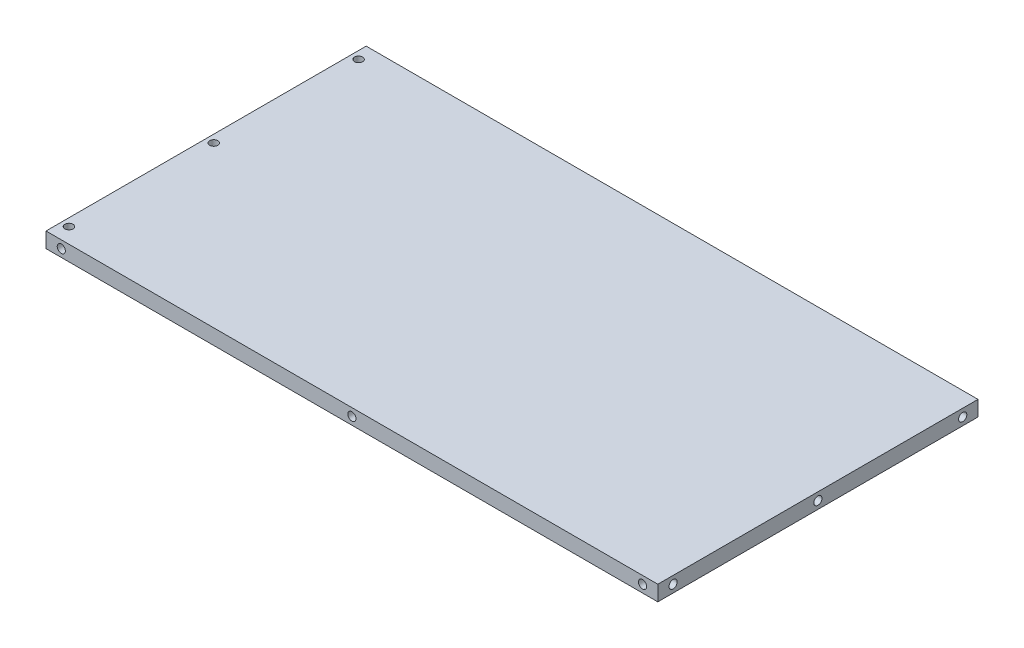
SolidWorks part; units mm, degrees
material "Oak"
ref_plane "Front Plane" through (0, 0, 0) normal (0, 0, 1) x (1, 0, 0)
ref_plane "Top Plane" through (0, 0, 0) normal (0, 1, 0) x (1, 0, 0)
ref_plane "Right Plane" through (0, 0, 0) normal (1, 0, 0) x (0, 0, -1)
sketch "Sketch1" plane through (0, 0, 0) normal (0, 1, 0) x (1, 0, 0)
  line L1 (-300, -157) -> (300, -157)
  line L2 (-300, -157) -> (-300, 157)
  line L3 (-300, 157) -> (300, 157)
  line L4 (300, -157) -> (300, 157)
  line L5 (-300, -157) -> (300, 157) construction
  line L6 (-300, 157) -> (300, -157) construction
  point P0 (0, 0)
  dimension "D1" = 600
  dimension "D2" = 314
extrude "Boss-Extrude1" add sketch "Sketch1" along normal blind 15
sketch "Sketch2" plane through (0, 15, 0) normal (0, 1, 0) x (1, 0, 0)
  line L0 (-285, 157) -> (-285, -157) construction
  line L1 (300, 157) -> (-300, 157) construction
  line L2 (-300, -157) -> (300, -157) construction
  line L3 (-300, 157) -> (-300, -157) construction
  line L4 (-300, 157) -> (-285, 157) construction
  line L5 (-292.5, 157) -> (-292.5, 146) construction
  line L6 (-300, -142) -> (-285, -142) construction
  circle A0 centre (-292.5, 142) radius 4
  dimension "D1" = 15
  dimension "D4" = 8
  dimension "D2" = 15
  dimension "D3" = 11
extrude "Cut-Extrude1" cut sketch "Sketch2" against normal blind 10
pattern_linear "LPattern1" count 3 spacing 142 along (0, 0, 1) of "Cut-Extrude1"
sketch "Sketch3" plane through (0, 0, 157) normal (0, 0, 1) x (1, 0, 0)
  line L0 (285, 15) -> (285, 0) construction
  line L1 (-300, 15) -> (300, 15) construction
  line L2 (-300, 0) -> (300, 0) construction
  line L3 (-300, 7.5) -> (-289, 7.5) construction
  line L4 (-300, 15) -> (-300, 0) construction
  line L5 (300, 15) -> (300, 0) construction
  circle A0 centre (-285, 7.5) radius 4
  dimension "D1" = 8
  dimension "D2" = 11
  dimension "D3" = 15
extrude "Cut-Extrude2" cut sketch "Sketch3" against normal blind 10
pattern_linear "LPattern2" count 3 spacing 285 along (1, 0, 0) of "Cut-Extrude2"
sketch "Sketch4" plane through (300, 0, 0) normal (1, 0, 0) x (0, 0, -1)
  line L0 (-157, 7.5) -> (-146, 7.5) construction
  line L2 (-157, 15) -> (-157, 0) construction
  line L3 (142, 15) -> (142, 0) construction
  line L4 (-157, 15) -> (157, 15) construction
  line L5 (-157, 0) -> (157, 0) construction
  line L6 (157, 15) -> (157, 0) construction
  circle A0 centre (-142, 7.5) radius 4
  dimension "D1" = 8
  dimension "D2" = 11
  dimension "D3" = 15
extrude "Cut-Extrude3" cut sketch "Sketch4" against normal blind 10
pattern_linear "LPattern3" count 3 spacing 142 along (0, 0, -1) of "Cut-Extrude3"
mirror "Mirror1" about plane through (0, 0, 0) normal (0, 0, 1) of "LPattern2", "Cut-Extrude2"
equation "\"A\"= 600mm"
equation "\"B\"= 400mm - ( 4 * \"C\" ) - ( 2 * 13mm )"
equation "\"C\"= 15mm"
equation "\"D1@Sketch1\"=\"A\""
equation "\"D2@Sketch1\"=\"B\""
equation "\"D1@Boss-Extrude1\"=\"C\""
equation "\"D1@Sketch2\"=\"C\""
